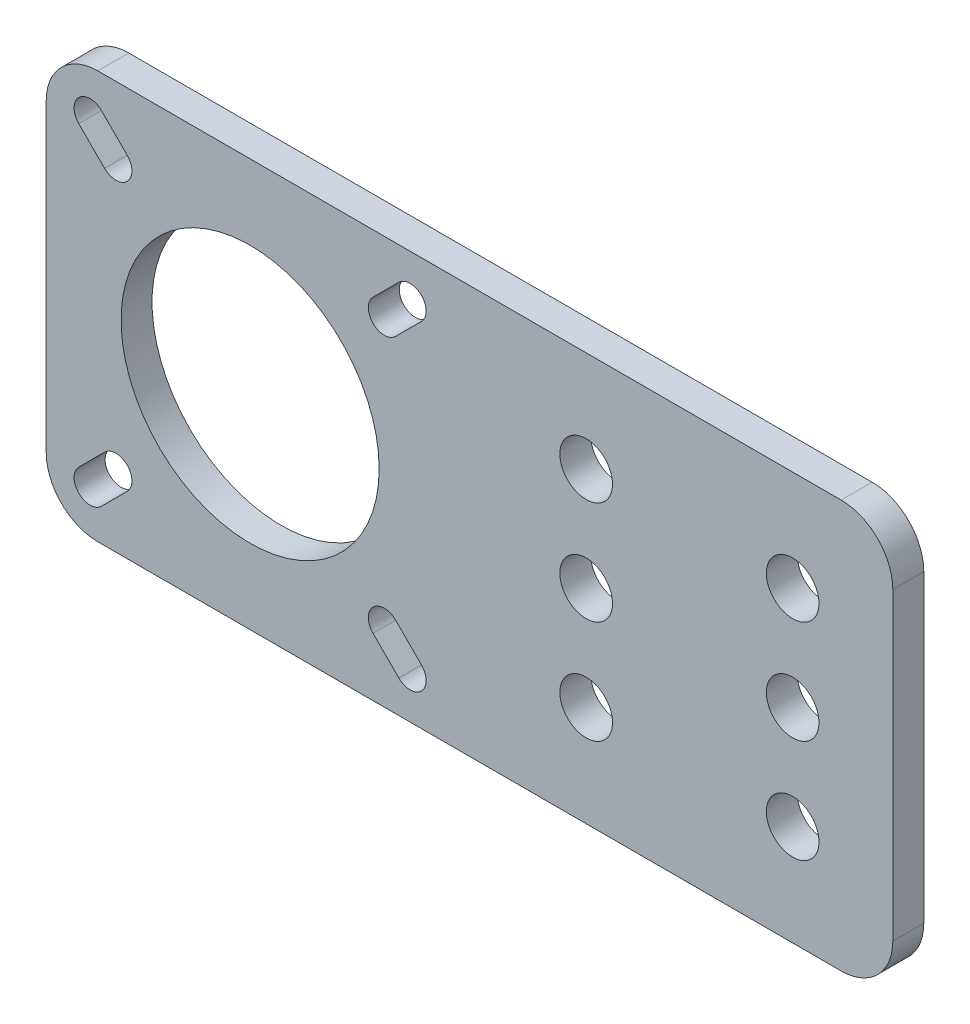
SolidWorks part; units mm, degrees
ref_plane "Front Plane" through (0, 0, 0) normal (0, 0, 1) x (1, 0, 0)
ref_plane "Top Plane" through (0, 0, 0) normal (0, 1, 0) x (1, 0, 0)
ref_plane "Right Plane" through (0, 0, 0) normal (1, 0, 0) x (0, 0, -1)
sketch "Sketch1" plane through (0, 0, 0) normal (0, 0, 1) x (1, 0, 0)
  line L0 (0, 39.5) -> (39.5, 0) construction
  line L1 (0, 0) -> (82, 0)
  line L2 (0, 0) -> (0, 39.5)
  line L3 (0, 39.5) -> (82, 39.5)
  line L4 (82, 0) -> (82, 39.5)
  line L5 (0, 0) -> (39.5, 39.5) construction
  line L6 (4.25, 35.25) -> (6.75, 32.75) construction
  line L7 (5.346, 36.346) -> (7.846, 33.846)
  line L8 (3.154, 34.154) -> (5.654, 31.654)
  line L9 (19.75, 39.5) -> (19.75, 0) construction
  line L10 (0, 19.75) -> (39.5, 19.75) construction
  line L11 (35.25, 35.25) -> (32.75, 32.75) construction
  line L12 (34.154, 36.346) -> (31.654, 33.846)
  line L13 (36.346, 34.154) -> (33.846, 31.654)
  line L14 (35.25, 4.25) -> (32.75, 6.75) construction
  line L15 (34.154, 3.154) -> (31.654, 5.654)
  line L16 (36.346, 5.346) -> (33.846, 7.846)
  line L17 (4.25, 4.25) -> (6.75, 6.75) construction
  line L18 (5.346, 3.154) -> (7.846, 5.654)
  line L19 (3.154, 5.346) -> (5.654, 7.846)
  line L20 (39.5, 39.5) -> (39.5, 0) construction
  line L21 (52.3, 39.5) -> (52.3, 0) construction
  line L22 (62.3, 39.5) -> (62.3, 0) construction
  circle A0 centre (19.75, 19.75) radius 12.5
  arc A1 (5.346, 36.346) -> (3.154, 34.154) centre (4.25, 35.25) ccw
  arc A2 (5.654, 31.654) -> (7.846, 33.846) centre (6.75, 32.75) ccw
  arc A3 (34.154, 36.346) -> (36.346, 34.154) centre (35.25, 35.25) cw
  arc A4 (33.846, 31.654) -> (31.654, 33.846) centre (32.75, 32.75) cw
  arc A5 (34.154, 3.154) -> (36.346, 5.346) centre (35.25, 4.25) ccw
  arc A6 (33.846, 7.846) -> (31.654, 5.654) centre (32.75, 6.75) ccw
  arc A7 (5.346, 3.154) -> (3.154, 5.346) centre (4.25, 4.25) cw
  arc A8 (5.654, 7.846) -> (7.846, 5.654) centre (6.75, 6.75) cw
  circle A9 centre (52.3, 19.75) radius 2.55
  circle A10 centre (52.3, 29.75) radius 2.55
  circle A11 centre (52.3, 9.75) radius 2.55
  circle A12 centre (72.3, 9.75) radius 2.55
  circle A13 centre (72.3, 19.75) radius 2.55
  circle A14 centre (72.3, 29.75) radius 2.55
  point P11 (5.5, 34)
  point P22 (34, 34)
  point P29 (34, 5.5)
  point P36 (5.5, 5.5)
  dimension "D5" = 25
  dimension "D8" = 35.25
  dimension "D9" = 5.1
  dimension "D1" = 82
  dimension "D2" = 39.5
  dimension "D3" = 45
  dimension "D4" = 45
  dimension "D6" = 3.1
  dimension "D7" = 32.75
  dimension "D10" = 32.55
  dimension "D11" = 10
  dimension "D12" = 10
  dimension "D13" = 10
extrude "Boss-Extrude1" add sketch "Sketch1" along normal blind 3
fillet "Fillet1" radius 5 4 edges at (0, 0, 1.5) (82, 0, 1.5) (82, 39.5, 1.5) (0, 39.5, 1.5)
